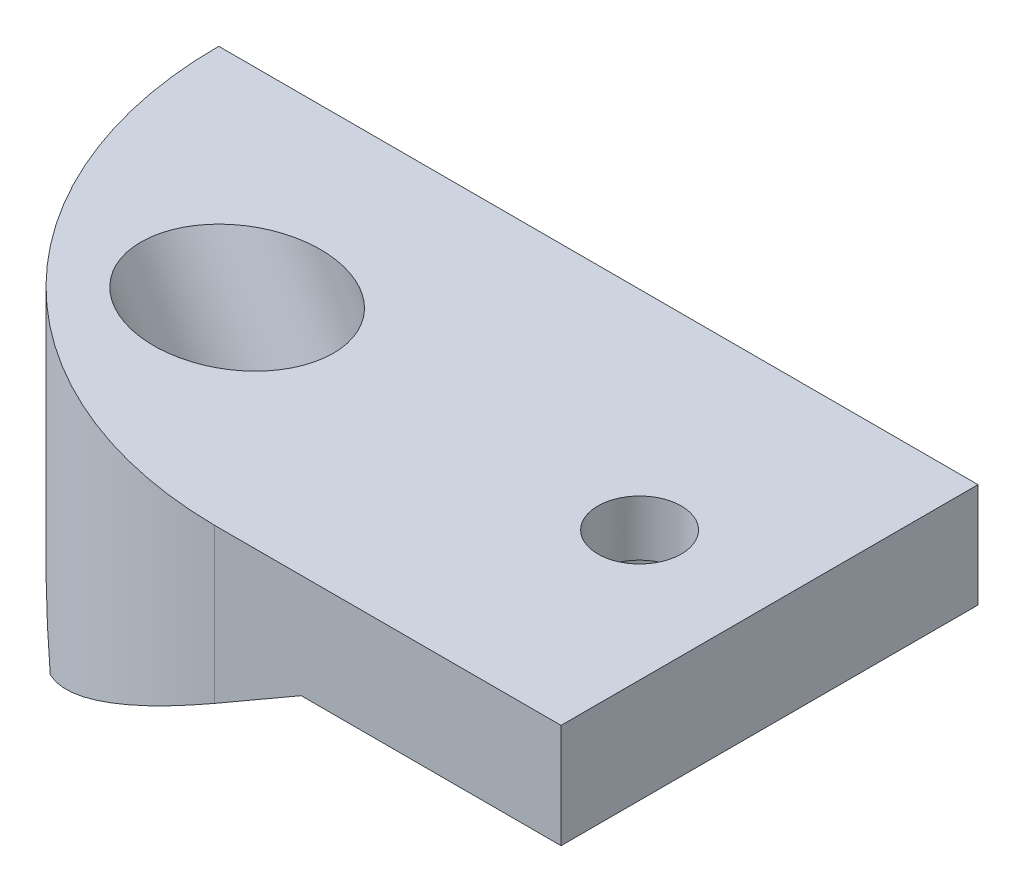
SolidWorks part; units mm, degrees
ref_plane "Plano frontal" through (0, 0, 0) normal (0, 0, 1) x (1, 0, 0)
ref_plane "Plano superior" through (0, 0, 0) normal (0, 1, 0) x (1, 0, 0)
ref_plane "Plano direito" through (0, 0, 0) normal (1, 0, 0) x (0, 0, -1)
sketch "Esboço1" plane through (0, 0, 0) normal (0, 1, 0) x (1, 0, 0)
  line L5 (-15, -15) -> (15, -15)
  line L6 (-15, -15) -> (-15, 15)
  line L7 (-15, 15) -> (15, 15)
  line L8 (15, -15) -> (15, 15)
  line L9 (-15, -15) -> (15, 15) construction
  line L10 (-15, 15) -> (15, -15) construction
  point P0 (0, 0)
  dimension "D1" = 30
  dimension "D2" = 30
extrude "Ressalto-extrusão1" add sketch "Esboço1" along normal blind 22.775
sketch "Esboço2" plane through (0, 0, 15) normal (0, 0, 1) x (1, 0, 0)
  line L7 (-15, 0) -> (15, 17.3205)
  line L8 (15, 22.775) -> (15, 0) construction
  line L9 (15, 17.3205) -> (15, 0)
  line L10 (15, 0) -> (-15, 0)
  line L11 (-15, 22.775) -> (15, 22.775) construction
  dimension "D1" = 30
extrude "Corte-extrusão1" cut sketch "Esboço2" against normal through all
sketch "Esboço3" plane through (-3.75, 6.4952, 0) normal (0.5, -0.866, 0) x (0.866, 0.5, 0)
  line L5 (21.6506, 15) -> (-12.9904, 15) construction
  line L7 (-10.6699, 15) -> (19.3301, 15)
  line L8 (-10.6699, 15) -> (-10.6699, -15)
  line L9 (-10.6699, -15) -> (19.3301, -15)
  line L10 (19.3301, 15) -> (19.3301, -15)
  line L11 (-10.6699, 15) -> (19.3301, -15) construction
  line L12 (-10.6699, -15) -> (19.3301, 15) construction
  line L13 (21.6506, -15) -> (21.6506, 15) construction
  point P0 (4.3301, 0)
  point P7 (21.6506, 0)
  point P12 (4.3301, 15)
  point P15 (19.3301, 0)
  dimension "D1" = 30
  dimension "D2" = 30
extrude "Corte-extrusão2" cut sketch "Esboço3" against normal through all flip side to cut
sketch "Esboço4" plane through (0, 0, 15) normal (0, 0, 1) x (1, 0, 0)
  line L0 (-25.4697, 22.775) -> (-15, 4.641)
  line L1 (-25.4697, 22.775) -> (-15, 22.775)
  line L2 (-15, 22.775) -> (9.1714, 22.775) construction
  line L3 (-15, 4.641) -> (-12.9904, 1.1603) construction
  line L4 (-15, 22.775) -> (-15, 4.641) construction
  line L5 (-15, 22.775) -> (-15, 4.641)
extrude "Ressalto-extrusão2" add sketch "Esboço4" against normal blind 30
sketch "Esboço5" plane through (-3.75, 6.4952, 0) normal (0.5, -0.866, 0) x (-0.866, -0.5, 0)
  circle A0 centre (-4.3301, 0) radius 3.95
  dimension "D1" = 7.9
extrude "Corte-extrusão3" cut sketch "Esboço5" against normal through all
sketch "Esboço6" plane through (0, 0, 15) normal (0, 0, 1) x (1, 0, 0)
  line L0 (12.9904, 16.1603) -> (-21.6506, 16.1603) construction
  line L2 (-25.4697, 22.775) -> (-12.9904, 1.1603) construction
  line L3 (-2.0096, 16.1603) -> (-2.0096, 22.775) construction
  line L5 (-25.4697, 22.775) -> (9.1714, 22.775) construction
  dimension "D1" = 15
sketch "Esboço8" plane through (-3.75, 6.4952, 0) normal (0.5, -0.866, 0) x (0.866, 0.5, 0)
  circle A0 centre (4.3301, 0) radius 6
  dimension "D1" = 12
extrude "Corte-extrusão5" cut sketch "Esboço8" against normal blind 25 from offset 8 offset against normal yes
sketch "Esboço16" plane through (0, 0, 15) normal (0, 0, 1) x (1, 0, 0)
  line L0 (9.1714, 22.775) -> (30.1571, 22.775)
  line L1 (30.1571, 22.775) -> (30.1571, 15.275)
  line L2 (12.9904, 16.1603) -> (-12.9904, 1.1603) construction
  line L3 (30.1571, 15.275) -> (11.4571, 15.275)
  line L6 (9.1714, 22.775) -> (11.4571, 15.275)
  dimension "D1" = 18.7
  dimension "D2" = 7.5
extrude "Ressalto-extrusão6" add sketch "Esboço16" against normal up to surface (30 mm away) up to face at (-4.0746, 15.7176, -15)
sketch "Esboço17" plane through (0, 22.775, 0) normal (0, 1, 0) x (1, 0, 0)
  line L0 (5.222, -14.9985) -> (5.222, -42.5265)
  line L1 (5.222, -42.5265) -> (-49.9141, -42.5265)
  line L2 (-49.9141, -42.5265) -> (-49.9141, 15)
  line L4 (30.1571, 15) -> (-25.4697, 15) construction
  line L5 (-49.9141, 15) -> (-24.475, 15)
  arc A0 (-24.4735, 14.697) -> (5.222, -14.9985) centre (5.525, 15) ccw construction
  arc A1 (-24.475, 15) -> (5.222, -14.9985) centre (5.525, 15) ccw
extrude "Corte-extrusão11" cut sketch "Esboço17" against normal blind 26
sketch "Esboço19" plane through (0, 15.275, 0) normal (0, -1, 0) x (1, 0, 0)
  line L0 (11.4571, -15) -> (11.4571, 15) construction
  circle A0 centre (20.8071, 0) radius 6.35
  point P5 (27.1571, 0)
  point P6 (14.4571, 0)
  dimension "D1" = 12.7
  dimension "D2" = 3
extrude "Corte-extrusão12" cut sketch "Esboço19" against normal blind 3.5
sketch "Esboço20" plane through (0, 18.775, 0) normal (0, -1, 0) x (1, 0, 0)
  circle A0 centre (20.8071, 0) radius 3
  dimension "D1" = 6
extrude "Corte-extrusão13" cut sketch "Esboço20" against normal blind 26
